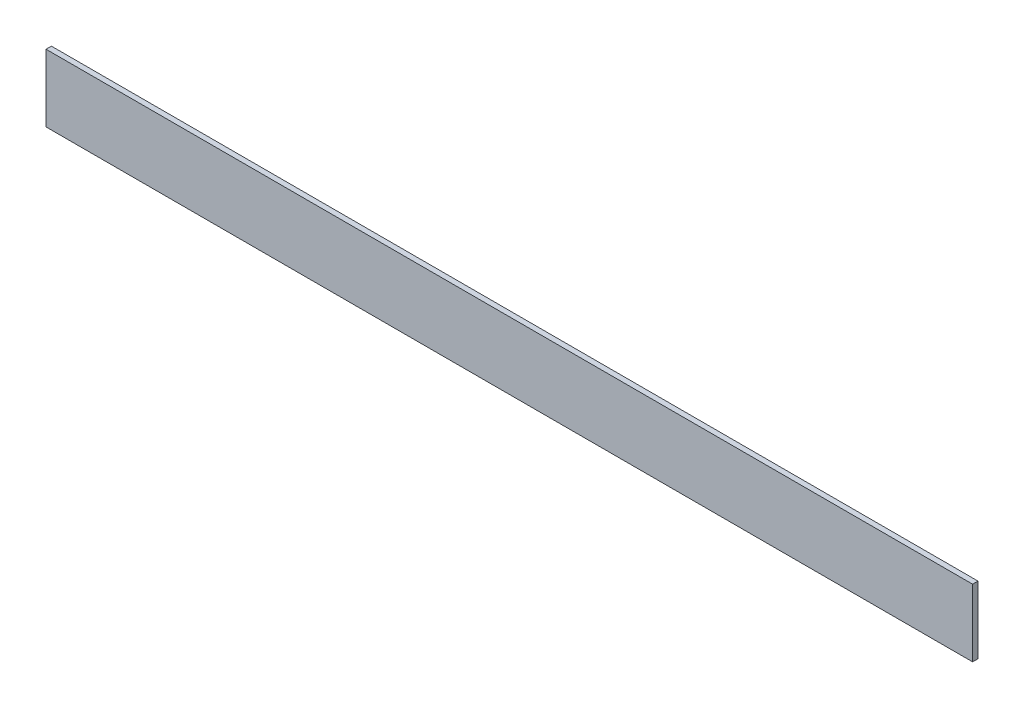
SolidWorks part; units mm, degrees
ref_plane "Спереди" through (0, 0, 0) normal (0, 0, 1) x (1, 0, 0)
ref_plane "Сверху" through (0, 0, 0) normal (0, 1, 0) x (1, 0, 0)
ref_plane "Справа" through (0, 0, 0) normal (1, 0, 0) x (0, 0, -1)
sketch "Эскиз2" plane through (0, 0, 0) normal (1, 0, 0) x (0, 0, -1)
  line L1 (0, 0) -> (2, 0)
  line L2 (0, 0) -> (0, 25)
  line L3 (0, 25) -> (2, 25)
  line L4 (2, 0) -> (2, 25)
extrude "Бобышка-Вытянуть1" add sketch "Эскиз2" along normal blind 344.2
